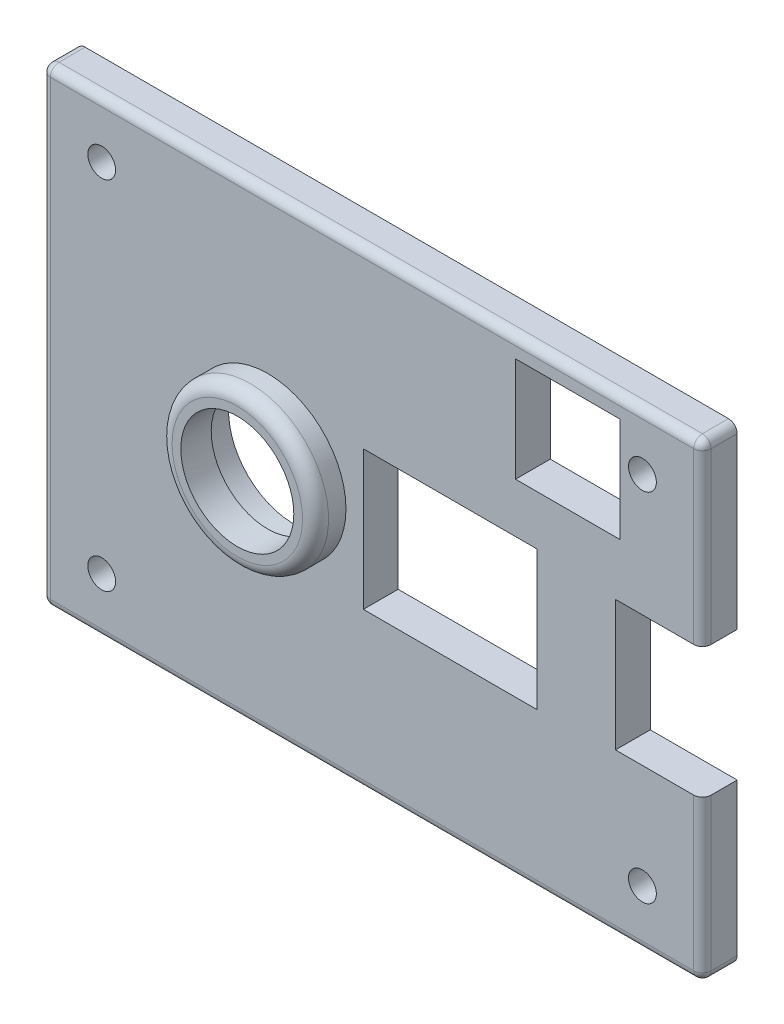
SolidWorks part; units mm, degrees
ref_plane "Front Plane" through (0, 0, 0) normal (0, 0, 1) x (1, 0, 0)
ref_plane "Top Plane" through (0, 0, 0) normal (0, 1, 0) x (1, 0, 0)
ref_plane "Right Plane" through (0, 0, 0) normal (1, 0, 0) x (0, 0, -1)
sketch "Enclosure Top Sketch" plane through (0, 0, 0) normal (0, 0, 1) x (1, 0, 0)
  line L1 (-38, 27) -> (38, 27)
  line L2 (-38, 27) -> (-38, -27)
  line L3 (-38, -27) -> (38, -27)
  line L4 (38, 27) -> (38, -27)
  line L5 (-38, 27) -> (38, -27) construction
  line L6 (-38, -27) -> (38, 27) construction
  point P1 (0, 0)
  dimension "D1" = 54
  dimension "D2" = 76
extrude "Enclosure Top Feature" add sketch "Enclosure Top Sketch" along normal blind 4
sketch "Screw Holes Sketch" plane through (0, 0, 4) normal (0, 0, 1) x (1, 0, 0)
  line L4 (-38, 27) -> (-38, -27) construction
  line L5 (38, 27) -> (-38, 27) construction
  line L6 (38, -27) -> (38, 27) construction
  line L7 (-38, -27) -> (38, -27) construction
  circle A0 centre (-31.1, 20.5) radius 1.6
  circle A1 centre (31.1, 20.5) radius 1.6
  circle A2 centre (31.1, -20.5) radius 1.6
  circle A3 centre (-31.1, -20.5) radius 1.6
  dimension "D1" = 6.9
  dimension "D3" = 6.5
  dimension "D4" = 6.9
  dimension "D5" = 6.5
  dimension "D6" = 6.5
  dimension "D2" = 6.5
  dimension "D7" = 6.9
  dimension "D8" = 6.9
extrude "Screw Holes Feature" cut sketch "Screw Holes Sketch" against normal through all
sketch "Camera + Light Hole Sketch" plane through (0, 0, 4) normal (0, 0, 1) x (1, 0, 0)
  line L0 (38, -27) -> (38, 27) construction
  line L5 (-38, 27) -> (-38, -27) construction
  line L6 (-38, -27) -> (38, -27) construction
  line L7 (-1, 7) -> (19, 7)
  line L8 (-1, 7) -> (-1, -9)
  line L9 (-1, -9) -> (19, -9)
  line L10 (19, 7) -> (19, -9)
  line L11 (-1, 7) -> (19, -9) construction
  line L12 (-1, -9) -> (19, 7) construction
  line L13 (28, 6.5) -> (38, 6.5)
  line L14 (28, 6.5) -> (28, -8.5)
  line L15 (28, -8.5) -> (38, -8.5)
  line L16 (38, 6.5) -> (38, -8.5)
  line L17 (28, 6.5) -> (38, -8.5) construction
  line L18 (28, -8.5) -> (38, 6.5) construction
  line L19 (38, 27) -> (-38, 27) construction
  line L20 (16.5, 24.714) -> (28.5, 24.714)
  line L21 (16.5, 24.714) -> (16.5, 12.714)
  line L22 (16.5, 12.714) -> (28.5, 12.714)
  line L23 (28.5, 24.714) -> (28.5, 12.714)
  line L24 (16.5, 24.714) -> (28.5, 12.714) construction
  line L25 (16.5, 12.714) -> (28.5, 24.714) construction
  circle A2 centre (-13, -1) radius 7.5
  point P5 (9, -1)
  point P11 (33, -1)
  point P13 (22.5, 18.714)
  dimension "D1" = 25
  dimension "D8" = 15
  dimension "D9" = 10
  dimension "D2" = 26
  dimension "D3" = 16
  dimension "D4" = 20
  dimension "D5" = 22
  dimension "D6" = 0
  dimension "D7" = 0
  dimension "D10" = 0
  dimension "D11" = 9.5
  dimension "D12" = 2.286
  dimension "D13" = 12
  dimension "D14" = 12
extrude "Camera + Light Hole Feature " cut sketch "Camera + Light Hole Sketch" against normal through all
sketch "Filter Cover Sketch" plane through (0, 0, 4) normal (0, 0, -1) x (-1, 0, 0)
  circle A0 centre (12, 0) radius 9
extrude "Filter Cover Feature" add sketch "Filter Cover Sketch" against normal blind 3.5 contours A0
sketch "Filter Hole Sketch" plane through (0, 0, 4) normal (0, 0, 1) x (1, 0, 0)
  circle A0 centre (-12, 0) radius 6.5
extrude "Filter Hole Cut" cut sketch "Filter Hole Sketch" along normal blind 3.5
fillet "Fillet6" radius 1.5 1 edges at (-21, 0, 7.5)
fillet "Fillet7" radius 1 1 edges at (0, 27, 4)
fillet "Fillet8" radius 1 1 edges at (0, -27, 4)
fillet "Fillet9" radius 1 5 edges at (-38, 27, 1.5) (-38, 26.7071, 3.7071) (-38, -27, 1.5) (-38, -26.7071, 3.7071) (-38, 0, 4)
fillet "Fillet10" radius 1 3 edges at (38, 27, 1.5) (38, 26.7071, 3.7071) (38, 16.25, 4)
fillet "Fillet11" radius 1 3 edges at (38, -27, 1.5) (38, -26.7071, 3.7071) (38, -17.25, 4)
